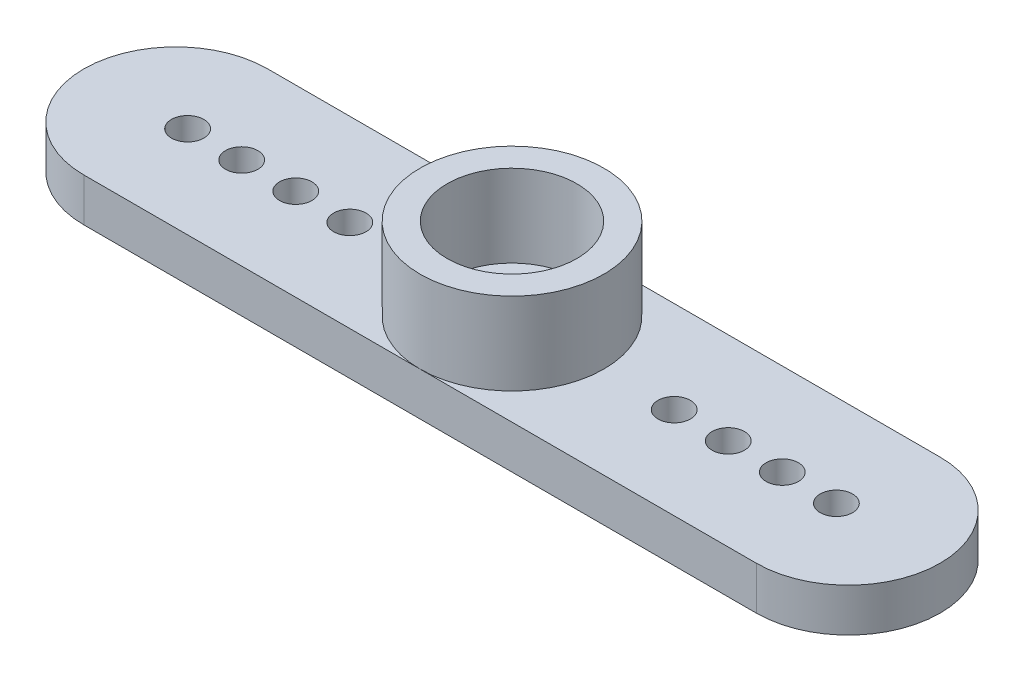
SolidWorks part; units mm, degrees
ref_plane "Спереди" through (0, 0, 0) normal (0, 0, 1) x (1, 0, 0)
ref_plane "Сверху" through (0, 0, 0) normal (0, 1, 0) x (1, 0, 0)
ref_plane "Справа" through (0, 0, 0) normal (1, 0, 0) x (0, 0, -1)
sketch "Эскиз1" plane through (0, 0, 0) normal (0, 1, 0) x (1, 0, 0)
  line L0 (0, 0) -> (31.1, 0) construction
  line L1 (0, 4.25) -> (31.1, 4.25)
  line L2 (0, -4.25) -> (31.1, -4.25)
  arc A0 (0, 4.25) -> (0, -4.25) centre (0, 0) ccw
  arc A1 (31.1, -4.25) -> (31.1, 4.25) centre (31.1, 0) ccw
  circle A2 centre (8.05, 0) radius 0.75
  circle A3 centre (23.05, 0) radius 0.75
  circle A4 centre (25.55, 0) radius 0.75
  circle A5 centre (28.05, 0) radius 0.75
  circle A6 centre (30.55, 0) radius 0.75
  circle A7 centre (5.55, 0) radius 0.75
  circle A8 centre (3.05, 0) radius 0.75
  circle A9 centre (0.55, 0) radius 0.75
  point P2 (15.55, 0)
  point P8 (-4.25, 0)
  point P9 (35.35, 0)
  dimension "D1" = 4.25
  dimension "D3" = 7.5
  dimension "D4" = 1.5
  dimension "D7" = 1.5
  dimension "D2" = 39.6
  dimension "D6" = 7.5
  dimension "D5" = 4
  dimension "D8" = 4
extrude "Бобышка-Вытянуть1" add sketch "Эскиз1" along normal blind 2
sketch "Эскиз2" plane through (0, 2, 0) normal (0, 1, 0) x (1, 0, 0)
  line L0 (-4.25, 0) -> (35.35, 0) construction
  circle A0 centre (15.55, 0) radius 4.25
  arc A1 (0, 4.25) -> (0, -4.25) centre (0, 0) ccw construction
  arc A2 (31.1, -4.25) -> (31.1, 4.25) centre (31.1, 0) ccw construction
  point P10 (15.55, 0)
  dimension "D1" = 8.5
extrude "Бобышка-Вытянуть2" add sketch "Эскиз2" along normal blind 3.8
sketch "Эскиз3" plane through (0, 5.8, 0) normal (0, 1, 0) x (1, 0, 0)
  circle A0 centre (15.55, 0) radius 3
  dimension "D1" = 6
extrude "Вырез-Вытянуть1" cut sketch "Эскиз3" against normal blind 3.8
